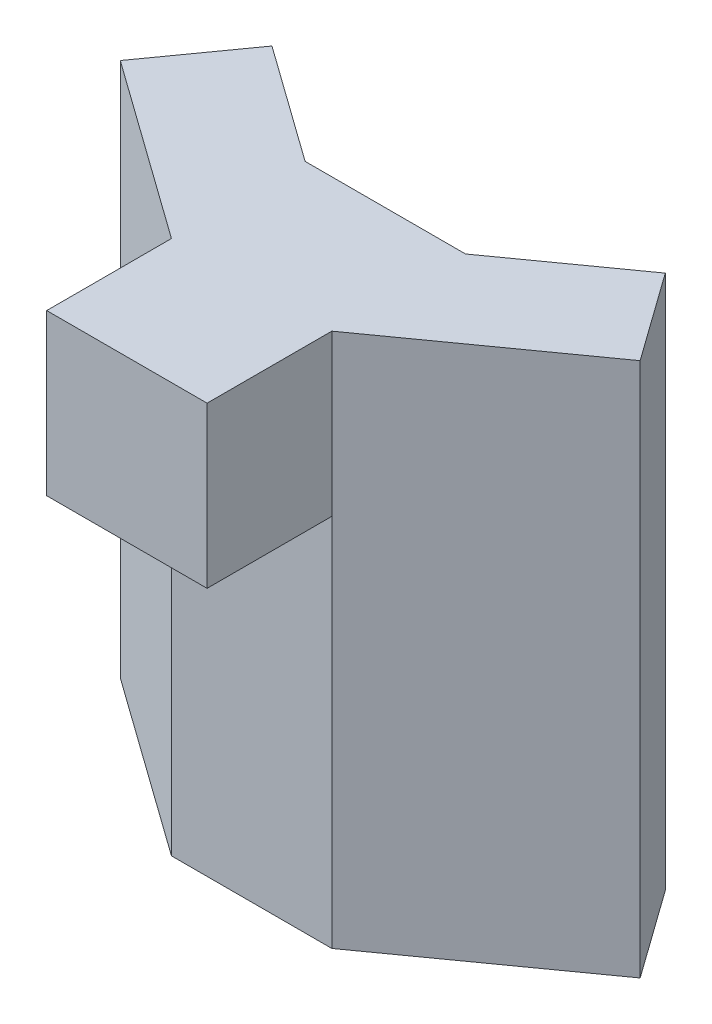
SolidWorks part; units mm, degrees
ref_plane "Front Plane" through (0, 0, 0) normal (0, 0, 1) x (1, 0, 0)
ref_plane "Top Plane" through (0, 0, 0) normal (0, 1, 0) x (1, 0, 0)
ref_plane "Right Plane" through (0, 0, 0) normal (1, 0, 0) x (0, 0, -1)
sketch "Sketch2" plane through (0, 0, 0) normal (0, 1, 0) x (1, 0, 0)
  line L0 (0, 0) -> (0, 75)
  line L2 (110.3637, 121.7563) -> (145.8533, 72.1429)
  line L3 (145.8533, 72.1429) -> (45, 0)
  line L4 (45, 0) -> (0, 0)
  line L5 (0, 75) -> (45, 75)
  line L6 (45, 75) -> (110.3637, 121.7563)
  point P3 (45, 75)
  point P7 (0, 0)
  dimension "D1" = 45
  dimension "D2" = 75
  dimension "D3" = 124
  dimension "D4" = 61
extrude "Boss-Extrude1" add sketch "Sketch2" along normal blind 300
mirror "Mirror1" about plane through (0, 0, 0) normal (1, 0, 0) of "Boss-Extrude1"
sketch "Sketch3" plane through (0, 0, 0) normal (0, 0, 1) x (1, 0, 0)
  line L0 (-45, 300) -> (-45, 0) construction
  line L1 (45, 300) -> (-45, 300)
  line L2 (45, 300) -> (45, 210)
  line L3 (45, 210) -> (-45, 210)
  line L4 (-45, 300) -> (-45, 210)
  line L5 (-45, 0) -> (45, 0) construction
  dimension "D1" = 210
extrude "Boss-Extrude2" add sketch "Sketch3" along normal blind 70
